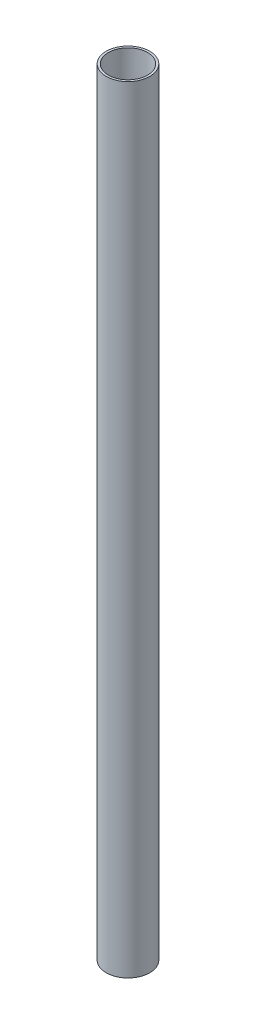
SolidWorks part; units mm, degrees
ref_plane "Front Plane" through (0, 0, 0) normal (0, 0, 1) x (1, 0, 0)
ref_plane "Top Plane" through (0, 0, 0) normal (0, 1, 0) x (1, 0, 0)
ref_plane "Right Plane" through (0, 0, 0) normal (1, 0, 0) x (0, 0, -1)
sketch "Sketch1" plane through (0, 0, 0) normal (0, 1, 0) x (1, 0, 0)
  circle A0 centre (0, 0) radius 2.25
  circle A1 centre (0, 0) radius 2.5
extrude "Boss-Extrude1" add sketch "Sketch1" along normal blind 89
sketch "Sketch2" plane through (0, 89, 0) normal (0, 1, 0) x (1, 0, 0)
  circle A0 centre (0, 0) radius 2.25
extrude "Boss-Extrude2" add sketch "Sketch2" against normal blind 66 from offset 5 separate body
